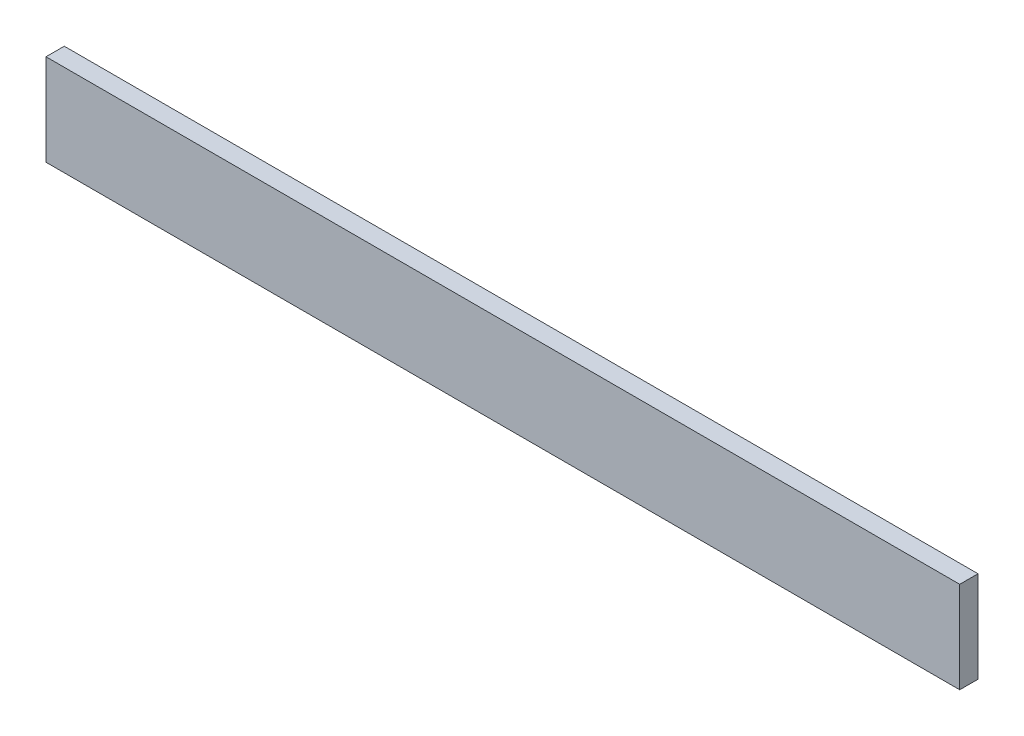
SolidWorks part; units mm, degrees
ref_plane "Front Plane" through (0, 0, 0) normal (0, 0, 1) x (1, 0, 0)
ref_plane "Top Plane" through (0, 0, 0) normal (0, 1, 0) x (1, 0, 0)
ref_plane "Right Plane" through (0, 0, 0) normal (1, 0, 0) x (0, 0, -1)
sketch "Sketch1" plane through (0, 0, 0) normal (0, 0, 1) x (1, 0, 0)
  line L1 (-317.5, -31.75) -> (317.5, -31.75)
  line L2 (-317.5, -31.75) -> (-317.5, 31.75)
  line L3 (-317.5, 31.75) -> (317.5, 31.75)
  line L4 (317.5, -31.75) -> (317.5, 31.75)
  line L5 (-317.5, -31.75) -> (317.5, 31.75) construction
  line L6 (-317.5, 31.75) -> (317.5, -31.75) construction
  point P0 (0, 0)
  dimension "D1" = 635
  dimension "D2" = 63.5
extrude "Boss-Extrude1" add sketch "Sketch1" along normal blind 12.7
